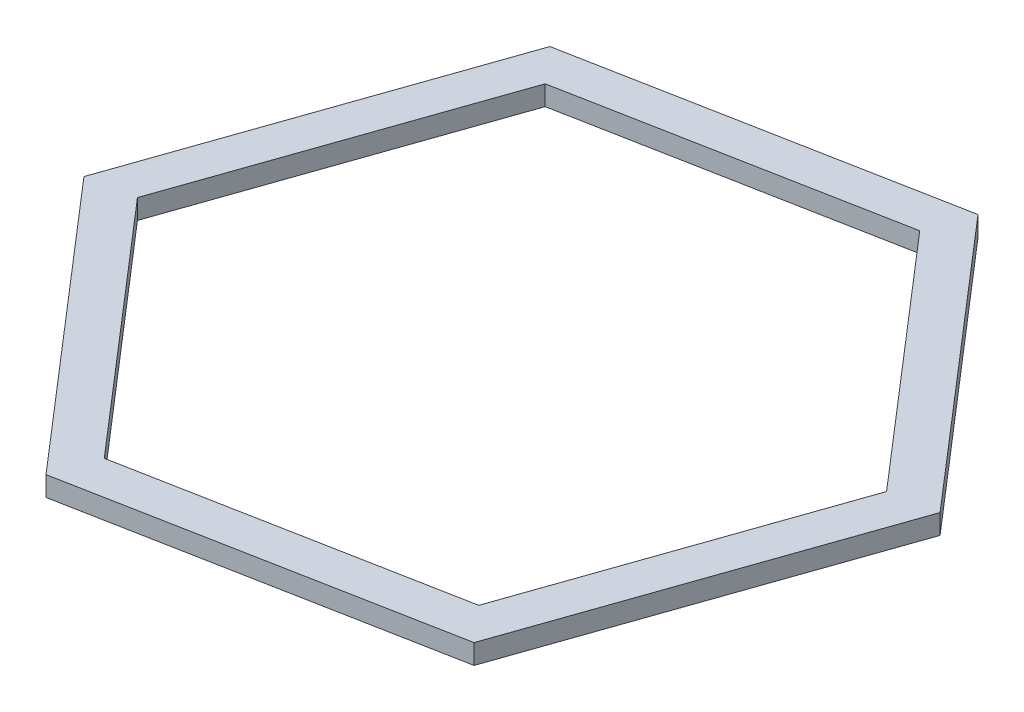
SolidWorks part; units mm, degrees
ref_plane "Front Plane" through (0, 0, 0) normal (0, 0, 1) x (1, 0, 0)
ref_plane "Top Plane" through (0, 0, 0) normal (0, 1, 0) x (1, 0, 0)
ref_plane "Right Plane" through (0, 0, 0) normal (1, 0, 0) x (0, 0, -1)
sketch "Sketch1" plane through (0, 0, 0) normal (0, 1, 0) x (1, 0, 0)
  line L1 (120.7144, -139.8592) -> (181.4788, 34.6121)
  line L2 (181.4788, 34.6121) -> (60.7644, 174.4713)
  line L3 (60.7644, 174.4713) -> (-120.7144, 139.8592)
  line L4 (-120.7144, 139.8592) -> (-181.4788, -34.6121)
  line L5 (-181.4788, -34.6121) -> (-60.7644, -174.4713)
  line L6 (-60.7644, -174.4713) -> (120.7144, -139.8592)
  line L11 (-100, 100) -> (100, -100) construction
  line L12 (-100, -100) -> (100, 100) construction
  circle A0 centre (0, 0) radius 159.9982 construction
  dimension "D3" = 184.75
extrude "Extrude-Thin3" add sketch "Sketch1" along normal blind 10 thin thin type one direction reverse wall 20
sketch "Sketch3" plane through (0, 10, 0) normal (0, 1, 0) x (1, 0, 0)
  line L0 (-60.7644, -174.4713) -> (60.7644, 174.4713)
  line L1 (-120.7144, 139.8592) -> (120.7144, -139.8592)
  line L2 (120.7144, -139.8592) -> (181.4788, 34.6121) construction
  line L3 (-181.4788, -34.6121) -> (181.4788, 34.6121)
  line L4 (181.4788, 34.6121) -> (60.7644, 174.4713) construction
